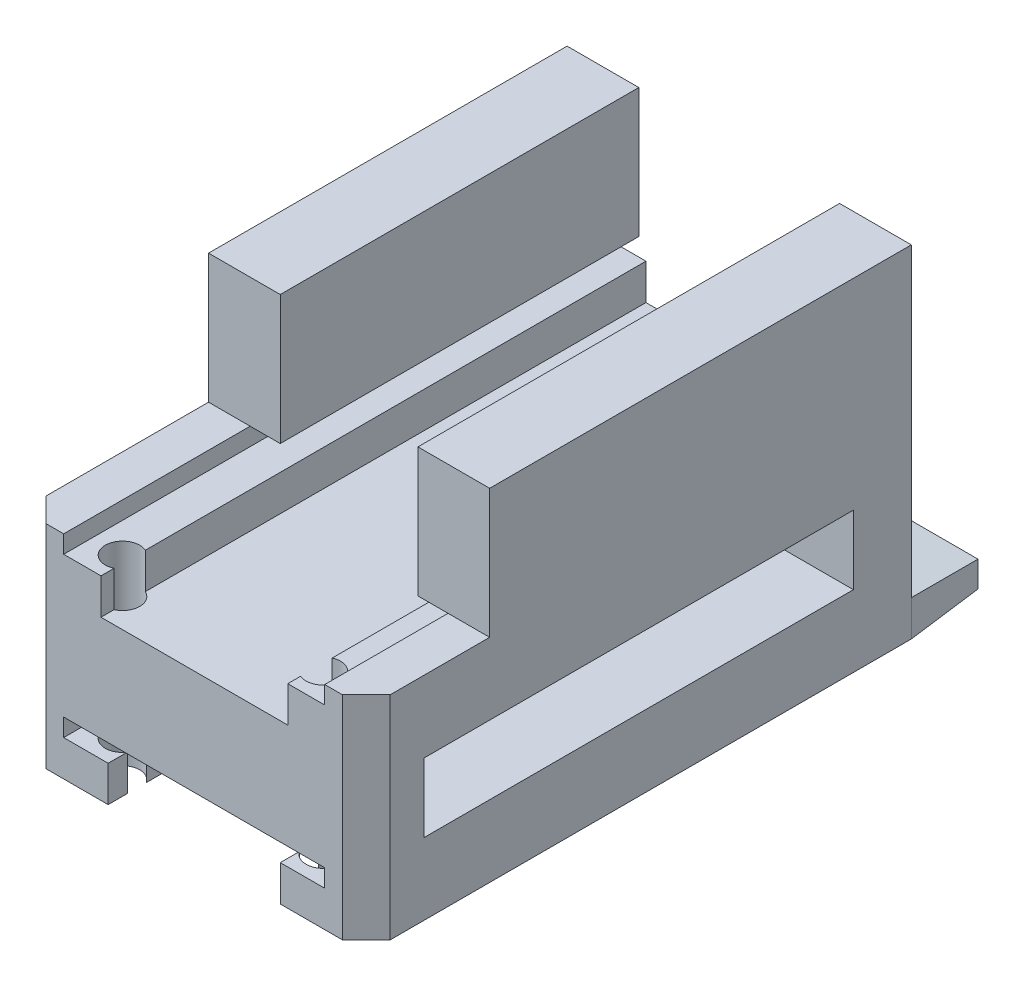
SolidWorks part; units mm, degrees
ref_plane "Front Plane" through (0, 0, 0) normal (0, 0, 1) x (1, 0, 0)
ref_plane "Top Plane" through (0, 0, 0) normal (0, 1, 0) x (1, 0, 0)
ref_plane "Right Plane" through (0, 0, 0) normal (1, 0, 0) x (0, 0, -1)
sketch "Sketch1" plane through (0, 0, 0) normal (0, 1, 0) x (1, 0, 0)
  line L0 (0, 25.4) -> (0, -25.4) construction
  line L1 (-15.24, -25.4) -> (15.24, -25.4)
  line L2 (-15.24, -25.4) -> (-15.24, 25.4)
  line L3 (-15.24, 25.4) -> (15.24, 25.4)
  line L4 (15.24, -25.4) -> (15.24, 25.4)
  line L5 (-15.24, -25.4) -> (15.24, 25.4) construction
  line L6 (-15.24, 25.4) -> (15.24, -25.4) construction
  line L7 (-11.43, 25.4) -> (-11.43, -25.4) construction
  line L8 (11.43, 25.4) -> (11.43, -25.4) construction
  line L9 (-15.24, 0) -> (15.24, 0) construction
  circle A0 centre (-8.89, -22.86) radius 1.524
  circle A1 centre (8.89, -22.86) radius 1.524
  circle A2 centre (8.89, 22.86) radius 1.524
  circle A3 centre (-8.89, 22.86) radius 1.524
  point P0 (0, 0)
  point P19 (0, 0)
  dimension "D4" = 3.048
  dimension "D5" = 45.72
  dimension "D6" = 17.78
  dimension "D1" = 50.8
  dimension "D2" = 30.48
  dimension "D3" = 22.86
extrude "Boss-Extrude1" add sketch "Sketch1" along normal blind 12.7 contours A3 | A2 | L1 L4 L3 L2 A1 A0 A2 A3
sketch "Sketch2" plane through (0, 0, 25.4) normal (0, 0, 1) x (1, 0, 0)
  line L0 (0, 0) -> (0, 12.7) construction
  line L1 (-15.24, 0) -> (15.24, 0) construction
  line L2 (-15.24, 12.7) -> (15.24, 12.7) construction
  line L3 (8.89, 12.7) -> (-8.89, 12.7)
  line L4 (-8.89, 12.7) -> (-8.89, 6.35)
  line L5 (8.89, 12.7) -> (8.89, 6.35)
  line L6 (-8.89, 6.35) -> (-11.557, 6.35)
  line L7 (8.89, 6.35) -> (11.557, 6.35)
  line L8 (-11.557, 6.35) -> (-11.557, 4.78)
  line L9 (11.557, 6.35) -> (11.557, 4.78)
  line L10 (-11.557, 4.78) -> (11.557, 4.78)
  point P14 (0, 4.78)
  dimension "D1" = 23.114
  dimension "D2" = 1.57
  dimension "D3" = 6.35
  dimension "D4" = 17.78
extrude "Cut-Extrude1" cut sketch "Sketch2" against normal through all
sketch "Sketch3" plane through (0, 12.7, 0) normal (0, 1, 0) x (1, 0, 0)
  line L1 (-15.24, -25.4) -> (1.9862, -25.4)
  line L2 (-15.24, -25.4) -> (-15.24, -8.89)
  line L3 (-15.24, -8.89) -> (1.9862, -8.89)
  line L4 (1.9862, -25.4) -> (1.9862, -8.89)
  line L5 (15.24, -25.4) -> (1.9862, -25.4)
  line L6 (15.24, -25.4) -> (15.24, -14.478)
  line L7 (15.24, -14.478) -> (1.9862, -14.478)
  line L8 (1.9862, -25.4) -> (1.9862, -14.478)
  line M6 (-8.89, -25.4) -> (-8.89, -24.384)
  line M8 (-15.24, 25.4) -> (-15.24, -25.4)
  line M9 (-15.24, -25.4) -> (-8.89, -25.4)
  dimension "D1" = 16.51
  dimension "D2" = 10.922
extrude "Cut-Extrude2" cut sketch "Sketch3" against normal up to surface (6.35 mm away) contours L3 M8 M9 M6 | L6 L7 L4 L5 | L1 L4 L3 M6 up to face at (-10.033, 6.35, 7.62)
sketch "Sketch4" plane through (0, 4.78, 0) normal (0, 1, 0) x (1, 0, 0)
  line L0 (11.557, 25.4) -> (11.557, -25.4) construction
  line L1 (-11.557, 25.4) -> (11.557, 25.4)
  line L2 (-11.557, 25.4) -> (-11.557, 6.35)
  line L3 (-11.557, 6.35) -> (11.557, 6.35)
  line L4 (11.557, 25.4) -> (11.557, 6.35)
  dimension "D1" = 19.05
extrude "Cut-Extrude3" cut sketch "Sketch4" against normal blind 3.175 contours L2 L1 L4 L3
sketch "Sketch6" plane through (0, 0, -25.4) normal (0, 0, -1) x (-1, 0, 0)
  line L12 (11.557, 6.35) -> (11.557, 1.605)
  line L13 (11.557, 1.605) -> (-11.557, 1.605)
  line L14 (-11.557, 1.605) -> (-11.557, 6.35)
  line L15 (-11.557, 6.35) -> (-8.89, 6.35)
  line L16 (-8.89, 6.35) -> (-8.89, 12.7)
  line L17 (-8.89, 12.7) -> (-15.24, 12.7)
  line L18 (-15.24, 12.7) -> (-15.24, 0)
  line L19 (-15.24, 0) -> (15.24, 0)
  line L20 (15.24, 0) -> (15.24, 12.7)
  line L21 (15.24, 12.7) -> (8.89, 12.7)
  line L22 (8.89, 12.7) -> (8.89, 6.35)
  line L23 (8.89, 6.35) -> (11.557, 6.35)
  line L24 (11.557, 6.35) -> (11.557, 1.605)
  line L25 (11.557, 1.605) -> (-11.557, 1.605)
  line L26 (-11.557, 1.605) -> (-11.557, 6.35)
  line L27 (-11.557, 6.35) -> (-8.89, 6.35)
  line L28 (-8.89, 6.35) -> (-8.89, 12.7)
  line L29 (-8.89, 12.7) -> (-15.24, 12.7)
  line L30 (-15.24, 12.7) -> (-15.24, 0)
  line L31 (-15.24, 0) -> (15.24, 0)
  line L32 (15.24, 0) -> (15.24, 12.7)
  line L33 (15.24, 12.7) -> (8.89, 12.7)
  line L34 (8.89, 12.7) -> (8.89, 6.35)
  line L35 (8.89, 6.35) -> (11.557, 6.35)
  dimension "D1" = 0
extrude "Cut-Extrude4" cut sketch "Sketch6" against normal blind 2.54
sketch "Sketch7" plane through (0, 0, -6.35) normal (0, 0, -1) x (-1, 0, 0)
  line L0 (-7.015, 4.58) -> (-7.015, 3.13) construction
  line L1 (-11.557, 1.605) -> (-8.285, 1.605)
  line L2 (-11.557, 1.605) -> (-11.557, 4.78)
  line L3 (-11.557, 4.78) -> (-8.285, 4.78)
  line L4 (-8.285, 1.605) -> (-8.285, 4.78)
  line L5 (11.557, 1.605) -> (8.255, 1.605)
  line L6 (11.557, 1.605) -> (11.557, 4.78)
  line L7 (11.557, 4.78) -> (8.255, 4.78)
  line L8 (8.255, 1.605) -> (8.255, 4.78)
  line L9 (6.985, 3.13) -> (6.985, 4.38) construction
  line L10 (11.557, 4.78) -> (-11.557, 4.78) construction
  dimension "D1" = 1.27
  dimension "D2" = 1.27
extrude "Boss-Extrude2" add sketch "Sketch7" along normal up to surface (16.51 mm away) up to face at (0, 6.6175, -22.86)
sketch "Sketch8" plane through (0, 0, -6.35) normal (0, 0, -1) x (-1, 0, 0)
  line L4 (8.255, 1.605) -> (8.255, 4.78)
  line L5 (8.255, 4.78) -> (-8.285, 4.78)
  line L6 (-8.285, 4.78) -> (-8.285, 1.605)
  line L7 (-8.285, 1.605) -> (8.255, 1.605)
  line L8 (8.255, 1.605) -> (8.255, 4.78)
  line L9 (8.255, 4.78) -> (-8.285, 4.78)
  line L10 (-8.285, 4.78) -> (-8.285, 1.605)
  line L11 (-8.285, 1.605) -> (8.255, 1.605)
  dimension "D1" = 0
extrude "Cut-Extrude5" cut sketch "Sketch8" against normal through all both and the other way through all
sketch "Sketch9" plane through (0, 0, 0) normal (0, -1, 0) x (1, 0, 0)
  line L0 (-15.24, 25.4) -> (-15.24, -22.86) construction
  line L1 (-15.24, 20.27) -> (15.24, 20.27)
  line L2 (-15.24, 20.27) -> (-15.24, -17.73)
  line L3 (-15.24, -17.73) -> (15.24, -17.73)
  line L4 (15.24, 20.27) -> (15.24, -17.73)
  line L5 (15.24, 25.4) -> (15.24, -22.86) construction
  line L6 (0, 20.27) -> (0, 25.4) construction
  line L7 (-15.24, 25.4) -> (15.24, 25.4) construction
  line L8 (0, -17.73) -> (0, -22.86) construction
  line L9 (15.24, -22.86) -> (-15.24, -22.86) construction
  line L14 (-15.24, 25.4) -> (-15.24, -22.86)
  line L15 (-15.24, -22.86) -> (15.24, -22.86)
  line L16 (15.24, -22.86) -> (15.24, 25.4)
  line L17 (15.24, 25.4) -> (-15.24, 25.4)
  line L18 (-15.24, 25.4) -> (-15.24, -22.86)
  line L19 (-15.24, -22.86) -> (15.24, -22.86)
  line L20 (15.24, -22.86) -> (15.24, 25.4)
  line L21 (15.24, 25.4) -> (-15.24, 25.4)
  circle M11 centre (8.89, 22.86) radius 1.524
  circle M12 centre (-8.89, 22.86) radius 1.524
  line M13 (-15.24, 25.4) -> (-15.24, -22.86)
  line M14 (-15.24, -22.86) -> (15.24, -22.86)
  line M15 (15.24, -22.86) -> (15.24, 25.4)
  line M16 (15.24, 25.4) -> (-15.24, 25.4)
  dimension "D1" = 38
  dimension "D2" = 0
extrude "Boss-Extrude3" add sketch "Sketch9" along normal blind 6.1 contours L1 M13 M15 M16 M12 M11 | L3 M13 M14 M15
sketch "Sketch10" plane through (0, -6.1, 0) normal (0, -1, 0) x (1, 0, 0)
  line L1 (-15.24, 25.4) -> (15.24, 25.4)
  line L2 (-15.24, 25.4) -> (-15.24, -22.86)
  line L3 (-15.24, -22.86) -> (15.24, -22.86)
  line L4 (15.24, 25.4) -> (15.24, -22.86)
  circle A0 centre (8.89, 22.86) radius 1.524 construction
  circle A1 centre (-8.89, 22.86) radius 1.524 construction
  circle A2 centre (8.89, 22.86) radius 1.524
  circle A3 centre (-8.89, 22.86) radius 1.524
extrude "Boss-Extrude4" add sketch "Sketch10" along normal blind 6.35
sketch "Sketch11" plane through (0, 0, 25.4) normal (0, 0, 1) x (1, 0, 0)
  line L0 (0, -12.45) -> (0, 0) construction
  line L13 (15.24, -12.45) -> (-15.24, -12.45) construction
  line L14 (-11.557, -7.7002) -> (11.557, -7.7002)
  line L15 (11.557, -7.7002) -> (11.557, -9.275)
  line L16 (-11.557, -7.7002) -> (-11.557, -9.275)
  line L17 (11.557, -9.275) -> (7.62, -9.275)
  line L18 (-11.557, -9.275) -> (-7.62, -9.275)
  line L19 (7.62, -9.275) -> (7.62, -12.45)
  line L20 (-7.62, -9.275) -> (-7.62, -12.45)
  line L21 (7.62, -12.45) -> (-7.62, -12.45)
  line L22 (11.557, 4.78) -> (11.557, 6.35) construction
  line L23 (11.557, 4.78) -> (11.557, 6.35)
  point P7 (0, -7.7002)
  dimension "D1" = 1.5748
  dimension "D2" = 3.175
  dimension "D3" = 15.24
extrude "Cut-Extrude7" cut sketch "Sketch11" against normal through all both
sketch "Sketch12" plane through (0, 0, -22.86) normal (0, 0, -1) x (-1, 0, 0)
  line L0 (15.24, -12.45) -> (15.24, 12.7) construction
  line L1 (15.24, -9.275) -> (-15.24, -9.275)
  line L2 (15.24, -9.275) -> (15.24, -12.45)
  line L3 (15.24, -12.45) -> (-15.24, -12.45)
  line L4 (-15.24, -9.275) -> (-15.24, -12.45)
  line L5 (-11.557, -9.275) -> (-7.62, -9.275) construction
  line L6 (-7.62, -9.275) -> (-7.62, -12.45) construction
  line L7 (7.62, -9.275) -> (7.62, -12.45) construction
  line L8 (7.62, -9.275) -> (7.62, -12.45)
  line L9 (-7.62, -9.275) -> (-7.62, -12.45)
  line M5 (11.557, -9.275) -> (7.62, -9.275)
  line M6 (7.62, -9.275) -> (7.62, -12.45)
  line M7 (7.62, -12.45) -> (15.24, -12.45)
  line M8 (15.24, -12.45) -> (15.24, 12.7)
  line M22 (-15.24, 12.7) -> (-15.24, -12.45)
  line M23 (-15.24, -12.45) -> (-7.62, -12.45)
  line M24 (-7.62, -12.45) -> (-7.62, -9.275)
  line M25 (-7.62, -9.275) -> (-11.557, -9.275)
extrude "Boss-Extrude5" add sketch "Sketch12" along normal blind 6.35 draft 4 contours L1 M25 M22 M23 M24 | L1 M8 M5 M6 M7
sketch "Sketch13" plane through (0, -12.45, 0) normal (0, -1, 0) x (1, 0, 0)
  line L0 (-11.8379, 29.02) -> (-10.6705, 27.8526) construction
  line L16 (-24.3384, 16.5195) -> (-23.171, 15.3521) construction
  line L17 (-10.6705, 27.8526) -> (-23.171, 15.3521) construction
  line L18 (-11.8379, 29.02) -> (-24.3384, 16.5195) construction
  line L23 (-14.047, 26.8109) -> (-17.6391, 30.403) construction
  line L24 (-12.7, 31.75) -> (-27.0684, 17.3816) construction
  line L27 (-22.1293, 18.7286) -> (-25.7214, 22.3207) construction
  line L29 (-22.1293, 18.7286) -> (-23.9253, 20.5247)
  line L30 (-15.8431, 28.6069) -> (-23.9253, 20.5247)
  line L31 (-14.047, 26.8109) -> (-15.8431, 28.6069)
  line L32 (-11.8379, 29.02) -> (-14.047, 26.8109)
  line L34 (-11.8379, 29.02) -> (-10.6705, 27.8526)
  line L35 (-10.6705, 27.8526) -> (-23.171, 15.3521)
  line L36 (-24.3384, 16.5195) -> (-23.171, 15.3521)
  line L37 (-22.1293, 18.7286) -> (-24.3384, 16.5195)
  line L38 (24.3384, 16.5195) -> (23.171, 15.3521) construction
  line L39 (22.1293, 18.7286) -> (25.7214, 22.3207) construction
  line L40 (12.7, 31.75) -> (27.0684, 17.3816) construction
  line L41 (14.047, 26.8109) -> (17.6391, 30.403) construction
  line L45 (11.8379, 29.02) -> (24.3384, 16.5195) construction
  line L46 (11.8379, 29.02) -> (10.6705, 27.8526) construction
  line L47 (10.6705, 27.8526) -> (23.171, 15.3521) construction
  line L48 (24.3384, 16.5195) -> (23.171, 15.3521)
  line L75 (22.1293, 18.7286) -> (23.9253, 20.5247)
  line L77 (15.8431, 28.6069) -> (23.9253, 20.5247)
  line L78 (14.047, 26.8109) -> (15.8431, 28.6069)
  line L79 (11.8379, 29.02) -> (14.047, 26.8109)
  line L80 (11.8379, 29.02) -> (10.6705, 27.8526)
  line L84 (10.6705, 27.8526) -> (23.171, 15.3521)
  line L175 (22.1293, 18.7286) -> (24.3384, 16.5195)
  line M10 (15.24, 25.4) -> (7.62, 25.4)
  line M15 (15.24, -22.86) -> (15.24, 25.4)
extrude "Cut-Extrude8" cut sketch "Sketch13" against normal through all contours L29 L37 L36 L35 L34 L32 L31 L30 | L175 L75 L77 L78 L79 L80 L84 L48 M10 M15 | L84 M10 M15
sketch "Sketch14" plane through (0, 12.7, 0) normal (0, 1, 0) x (1, 0, 0)
  line L4 (-8.89, 22.86) -> (-15.24, 22.86)
  line L5 (-15.24, 22.86) -> (-15.24, -8.89)
  line L6 (-15.24, -8.89) -> (-8.89, -8.89)
  line L7 (-8.89, -8.89) -> (-8.89, 22.86)
  line L8 (-8.89, 22.86) -> (-15.24, 22.86)
  line L9 (-15.24, 22.86) -> (-15.24, -8.89)
  line L10 (-15.24, -8.89) -> (-8.89, -8.89)
  line L11 (-8.89, -8.89) -> (-8.89, 22.86)
  line L12 (15.24, 22.86) -> (8.89, 22.86)
  line L13 (8.89, 22.86) -> (8.89, -14.478)
  line L14 (8.89, -14.478) -> (15.24, -14.478)
  line L15 (15.24, -14.478) -> (15.24, 22.86)
  line L16 (15.24, 22.86) -> (8.89, 22.86)
  line L17 (8.89, 22.86) -> (8.89, -14.478)
  line L18 (8.89, -14.478) -> (15.24, -14.478)
  line L19 (15.24, -14.478) -> (15.24, 22.86)
  dimension "D1" = 0
  dimension "D2" = 0
extrude "Boss-Extrude6" add sketch "Sketch14" along normal blind 5.08
